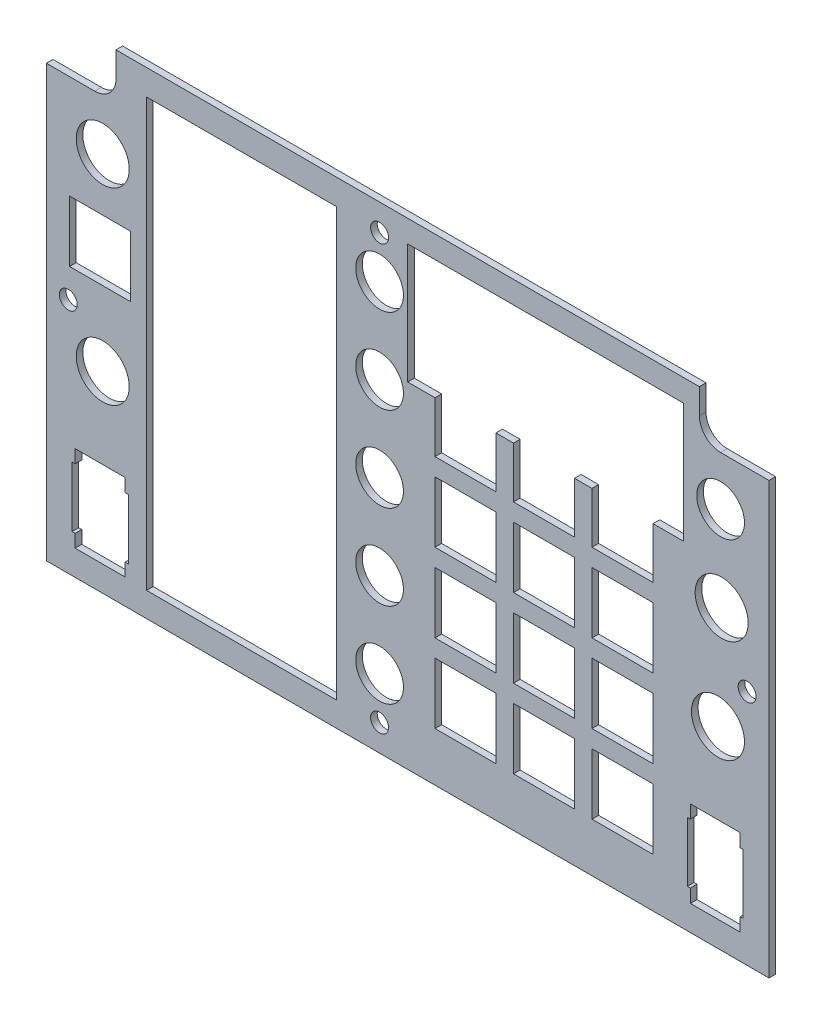
SolidWorks part; units mm, degrees
material "ABS PC"
ref_plane "Front Plane" through (0, 0, 0) normal (0, 0, 1) x (1, 0, 0)
ref_plane "Top Plane" through (0, 0, 0) normal (0, 1, 0) x (1, 0, 0)
ref_plane "Right Plane" through (0, 0, 0) normal (1, 0, 0) x (0, 0, -1)
sketch "Sketch1" plane through (0, 0, 0) normal (0, 0, 1) x (1, 0, 0)
  line L8 (58.2068, 169.534) -> (58.2068, 175.5665)
  line L9 (58.2068, 175.5665) -> (-81.4932, 175.5665)
  line L10 (-81.4932, 175.5665) -> (-81.4932, 169.534)
  line L11 (-86.5732, 164.454) -> (-98.162, 164.454)
  line L12 (-98.162, 164.454) -> (-98.162, 61.2665)
  line L13 (-98.162, 61.2665) -> (74.8755, 61.2665)
  line L14 (74.8755, 61.2665) -> (74.8755, 164.454)
  line L15 (74.8755, 164.454) -> (63.2868, 164.454)
  line L16 (58.2068, 169.534) -> (58.2068, 175.5665)
  line L17 (58.2068, 175.5665) -> (-81.4932, 175.5665)
  line L18 (-81.4932, 175.5665) -> (-81.4932, 169.534)
  line L19 (-86.5732, 164.454) -> (-98.162, 164.454)
  line L20 (-98.162, 164.454) -> (-98.162, 61.2665)
  line L21 (-98.162, 61.2665) -> (74.8755, 61.2665)
  line L22 (74.8755, 61.2665) -> (74.8755, 164.454)
  line L23 (74.8755, 164.454) -> (63.2868, 164.454)
  arc A2 (58.2068, 169.534) -> (63.2868, 164.454) centre (63.2868, 169.534) ccw
  arc A3 (-86.5732, 164.454) -> (-81.4932, 169.534) centre (-86.5732, 169.534) ccw
  arc A4 (58.2068, 169.534) -> (63.2868, 164.454) centre (63.2868, 169.534) ccw
  arc A5 (-86.5732, 164.454) -> (-81.4932, 169.534) centre (-86.5732, 169.534) ccw
  dimension "D1" = 0
extrude "Boss-Extrude1" add sketch "Sketch1" along normal blind 1.5875
sketch "Sketch2" plane through (0, 0, 1.5875) normal (0, 0, 1) x (1, 0, 0)
  line L4 (67.9868, 67.3295) -> (67.9868, 87.9695)
  line L5 (56.0468, 67.3295) -> (67.9868, 67.3295)
  line L6 (56.0468, 87.9695) -> (56.0468, 67.3295)
  line L7 (67.9868, 87.9695) -> (56.0468, 87.9695)
  line L8 (67.9868, 67.3295) -> (67.9868, 87.9695)
  line L9 (56.0468, 67.3295) -> (67.9868, 67.3295)
  line L10 (56.0468, 87.9695) -> (56.0468, 67.3295)
  line L11 (67.9868, 87.9695) -> (56.0468, 87.9695)
  line L26 (32.4893, 73.014) -> (47.0943, 73.014)
  line L27 (32.4893, 87.619) -> (32.4893, 73.014)
  line L28 (47.0943, 87.619) -> (32.4893, 87.619)
  line L29 (47.0943, 73.014) -> (47.0943, 87.619)
  line L30 (32.4893, 73.014) -> (47.0943, 73.014)
  line L31 (32.4893, 87.619) -> (32.4893, 73.014)
  line L32 (47.0943, 87.619) -> (32.4893, 87.619)
  line L33 (47.0943, 73.014) -> (47.0943, 87.619)
  line L34 (32.4893, 91.81) -> (47.0943, 91.81)
  line L35 (32.4893, 106.415) -> (32.4893, 91.81)
  line L36 (47.0943, 106.415) -> (32.4893, 106.415)
  line L37 (47.0943, 91.81) -> (47.0943, 106.415)
  line L38 (32.4893, 91.81) -> (47.0943, 91.81)
  line L39 (32.4893, 106.415) -> (32.4893, 91.81)
  line L40 (47.0943, 106.415) -> (32.4893, 106.415)
  line L41 (47.0943, 91.81) -> (47.0943, 106.415)
  line L42 (32.4893, 110.606) -> (47.0943, 110.606)
  line L43 (32.4893, 125.211) -> (32.4893, 110.606)
  line L44 (47.0943, 125.211) -> (32.4893, 125.211)
  line L45 (47.0943, 110.606) -> (47.0943, 125.211)
  line L46 (32.4893, 110.606) -> (47.0943, 110.606)
  line L47 (32.4893, 125.211) -> (32.4893, 110.606)
  line L48 (47.0943, 125.211) -> (32.4893, 125.211)
  line L49 (47.0943, 110.606) -> (47.0943, 125.211)
  line L51 (13.6933, 73.014) -> (28.2983, 73.014)
  line L52 (13.6933, 87.619) -> (13.6933, 73.014)
  line L53 (28.2983, 87.619) -> (13.6933, 87.619)
  line L54 (28.2983, 73.014) -> (28.2983, 87.619)
  line L55 (13.6933, 73.014) -> (28.2983, 73.014)
  line L56 (13.6933, 87.619) -> (13.6933, 73.014)
  line L57 (28.2983, 87.619) -> (13.6933, 87.619)
  line L58 (28.2983, 73.014) -> (28.2983, 87.619)
  line L59 (13.6933, 91.81) -> (28.2983, 91.81)
  line L60 (13.6933, 106.415) -> (13.6933, 91.81)
  line L61 (28.2983, 106.415) -> (13.6933, 106.415)
  line L62 (32.4893, 141.6095) -> (32.4893, 129.402)
  line L63 (28.2983, 141.6095) -> (32.4893, 141.6095)
  line L64 (28.2983, 129.402) -> (28.2983, 141.6095)
  line L65 (13.6933, 129.402) -> (28.2983, 129.402)
  line L66 (13.6933, 141.6095) -> (13.6933, 129.402)
  line L67 (9.5023, 141.6095) -> (13.6933, 141.6095)
  line L68 (9.5023, 129.402) -> (9.5023, 141.6095)
  line L69 (-5.1027, 129.402) -> (9.5023, 129.402)
  line L70 (-5.1027, 141.6095) -> (-5.1027, 129.402)
  line L71 (-11.6432, 141.6095) -> (-5.1027, 141.6095)
  line L72 (-11.6432, 170.2495) -> (-11.6432, 141.6095)
  line L73 (54.3968, 170.2495) -> (-11.6432, 170.2495)
  line L74 (54.3968, 141.6095) -> (54.3968, 170.2495)
  line L75 (47.0943, 141.6095) -> (54.3968, 141.6095)
  line L76 (47.0943, 129.402) -> (47.0943, 141.6095)
  line L77 (32.4893, 129.402) -> (47.0943, 129.402)
  line L78 (32.4893, 141.6095) -> (32.4893, 129.402)
  line L79 (28.2983, 141.6095) -> (32.4893, 141.6095)
  line L80 (28.2983, 129.402) -> (28.2983, 141.6095)
  line L81 (13.6933, 129.402) -> (28.2983, 129.402)
  line L82 (13.6933, 141.6095) -> (13.6933, 129.402)
  line L83 (9.5023, 141.6095) -> (13.6933, 141.6095)
  line L84 (9.5023, 129.402) -> (9.5023, 141.6095)
  line L85 (-5.1027, 129.402) -> (9.5023, 129.402)
  line L86 (-5.1027, 141.6095) -> (-5.1027, 129.402)
  line L87 (-11.6432, 141.6095) -> (-5.1027, 141.6095)
  line L88 (-11.6432, 170.2495) -> (-11.6432, 141.6095)
  line L89 (54.3968, 170.2495) -> (-11.6432, 170.2495)
  line L90 (54.3968, 141.6095) -> (54.3968, 170.2495)
  line L91 (47.0943, 141.6095) -> (54.3968, 141.6095)
  line L92 (47.0943, 129.402) -> (47.0943, 141.6095)
  line L93 (32.4893, 129.402) -> (47.0943, 129.402)
  line L94 (28.2983, 91.81) -> (28.2983, 106.415)
  line L95 (13.6933, 91.81) -> (28.2983, 91.81)
  line L96 (13.6933, 106.415) -> (13.6933, 91.81)
  line L97 (28.2983, 106.415) -> (13.6933, 106.415)
  line L98 (28.2983, 91.81) -> (28.2983, 106.415)
  line L99 (13.6933, 110.606) -> (28.2983, 110.606)
  line L100 (13.6933, 125.211) -> (13.6933, 110.606)
  line L101 (28.2983, 125.211) -> (13.6933, 125.211)
  line L102 (28.2983, 110.606) -> (28.2983, 125.211)
  line L103 (13.6933, 110.606) -> (28.2983, 110.606)
  line L104 (13.6933, 125.211) -> (13.6933, 110.606)
  line L105 (28.2983, 125.211) -> (13.6933, 125.211)
  line L106 (28.2983, 110.606) -> (28.2983, 125.211)
  line L107 (9.5023, 125.211) -> (-5.1027, 125.211)
  line L108 (9.5023, 110.606) -> (9.5023, 125.211)
  line L109 (-5.1027, 110.606) -> (9.5023, 110.606)
  line L110 (-5.1027, 125.211) -> (-5.1027, 110.606)
  line L111 (9.5023, 125.211) -> (-5.1027, 125.211)
  line L112 (9.5023, 110.606) -> (9.5023, 125.211)
  line L113 (-5.1027, 110.606) -> (9.5023, 110.606)
  line L114 (-5.1027, 125.211) -> (-5.1027, 110.606)
  line L115 (-5.1027, 91.81) -> (9.5023, 91.81)
  line L116 (-5.1027, 106.415) -> (-5.1027, 91.81)
  line L117 (9.5023, 106.415) -> (-5.1027, 106.415)
  line L118 (9.5023, 91.81) -> (9.5023, 106.415)
  line L119 (-5.1027, 91.81) -> (9.5023, 91.81)
  line L120 (-5.1027, 106.415) -> (-5.1027, 91.81)
  line L121 (9.5023, 106.415) -> (-5.1027, 106.415)
  line L122 (9.5023, 91.81) -> (9.5023, 106.415)
  line L123 (-5.1027, 73.014) -> (9.5023, 73.014)
  line L124 (-5.1027, 87.619) -> (-5.1027, 73.014)
  line L125 (9.5023, 87.619) -> (-5.1027, 87.619)
  line L126 (9.5023, 73.014) -> (9.5023, 87.619)
  line L127 (-5.1027, 73.014) -> (9.5023, 73.014)
  line L128 (-5.1027, 87.619) -> (-5.1027, 73.014)
  line L129 (9.5023, 87.619) -> (-5.1027, 87.619)
  line L130 (9.5023, 73.014) -> (9.5023, 87.619)
  line L131 (-78.0007, 139.689) -> (-92.6057, 139.689)
  line L132 (-78.0007, 125.084) -> (-78.0007, 139.689)
  line L133 (-92.6057, 125.084) -> (-78.0007, 125.084)
  line L134 (-92.6057, 139.689) -> (-92.6057, 125.084)
  line L135 (-78.0007, 139.689) -> (-92.6057, 139.689)
  line L136 (-78.0007, 125.084) -> (-78.0007, 139.689)
  line L137 (-92.6057, 125.084) -> (-78.0007, 125.084)
  line L138 (-92.6057, 139.689) -> (-92.6057, 125.084)
  line L139 (-74.1732, 67.1295) -> (-28.7112, 67.1295)
  line L140 (-74.1732, 169.4495) -> (-74.1732, 67.1295)
  line L141 (-28.7112, 169.4495) -> (-74.1732, 169.4495)
  line L142 (-28.7112, 67.1295) -> (-28.7112, 169.4495)
  line L143 (-74.1732, 67.1295) -> (-28.7112, 67.1295)
  line L144 (-74.1732, 169.4495) -> (-74.1732, 67.1295)
  line L145 (-28.7112, 169.4495) -> (-74.1732, 169.4495)
  line L146 (-28.7112, 67.1295) -> (-28.7112, 169.4495)
  line L147 (-79.3332, 67.3295) -> (-79.3332, 87.9695)
  line L148 (-91.2732, 67.3295) -> (-79.3332, 67.3295)
  line L149 (-91.2732, 87.9695) -> (-91.2732, 67.3295)
  line L150 (-79.3332, 87.9695) -> (-91.2732, 87.9695)
  line L151 (-79.3332, 67.3295) -> (-79.3332, 87.9695)
  line L152 (-91.2732, 67.3295) -> (-79.3332, 67.3295)
  line L153 (-91.2732, 87.9695) -> (-91.2732, 67.3295)
  line L154 (-79.3332, 87.9695) -> (-91.2732, 87.9695)
  circle A0 centre (-84.6682, 152.389) radius 6.35
  circle A1 centre (-84.6682, 107.304) radius 6.35
  circle A2 centre (63.5408, 132.3865) radius 6.35
  circle A3 centre (62.6518, 107.304) radius 6.35
  circle A10 centre (-18.3742, 77.7765) radius 5.715 construction
  circle A11 centre (-18.3742, 98.0965) radius 5.715 construction
  circle A12 centre (-18.3742, 118.4165) radius 5.715 construction
  circle A13 centre (-18.3742, 138.7365) radius 5.715 construction
  circle A14 centre (-18.3742, 159.0565) radius 5.715 construction
  circle A15 centre (-18.3742, 77.7765) radius 5.715
  circle A16 centre (-18.3742, 98.0965) radius 5.715
  circle A17 centre (-18.3742, 118.4165) radius 5.715
  circle A18 centre (-18.3742, 138.7365) radius 5.715
  circle A19 centre (-18.3742, 159.0565) radius 5.715
  circle A20 centre (63.2868, 152.7065) radius 5.715 construction
  circle A21 centre (63.2868, 152.7065) radius 5.715
  dimension "D1" = 12.7
  dimension "D2" = 0
  dimension "D3" = 0
  dimension "D4" = 0
  dimension "D5" = 0
  dimension "D6" = 0
  dimension "D7" = 0
  dimension "D8" = 0
  dimension "D9" = 0
  dimension "D10" = 0
  dimension "D11" = 0
  dimension "D12" = 0
  dimension "D13" = 0
  dimension "D14" = 0
  dimension "D15" = 0
extrude "Cut-Extrude1" cut sketch "Sketch2" against normal through all
hole_wizard "#6 Clearance Hole2" positions "Sketch5" profile "Sketch6" hole size "#6" standard "ANSI Inch" end condition through all
sketch "Sketch5" plane through (-11.6432, -6.6627, -3.175) normal (0, 0, -1) x (-1, 0, 0)
  point P0 (-81.28, 124.6982)
  point P3 (6.731, 175.8792)
  point P6 (81.28, 124.6982)
  point P9 (6.731, 74.2792)
sketch "Sketch6" plane through (69.6368, 118.0355, -3.175) normal (1, 0, 0) x (0, 1, 0)
  line L0 (0, 0) -> (0, 4.7625)
  line L1 (0, 4.7625) -> (2.1526, 4.7625)
  line L2 (2.1526, 4.7625) -> (2.1526, 0)
  line L3 (2.1526, 0) -> (0, 0)
  line L4 (0, -6.35) -> (0, 107.95) construction
  dimension "Thru Hole Dia." = 4.3053
  dimension "Thru Hole Depth" = 4.7625
sketch "Sketch7" plane through (0, 0, 1.5875) normal (0, 0, 1) x (1, 0, 0)
  line L1 (55.3386, 84.8302) -> (68.6714, 84.8302)
  line L2 (55.3386, 84.8302) -> (55.3386, 70.5174)
  line L3 (55.3386, 70.5174) -> (68.6714, 70.5174)
  line L4 (68.6714, 84.8302) -> (68.6714, 70.5174)
  line L5 (-78.4913, 70.4042) -> (-92.0203, 70.4042)
  line L6 (-78.4913, 70.4042) -> (-78.4913, 84.8288)
  line L7 (-78.4913, 84.8288) -> (-92.0203, 84.8288)
  line L8 (-92.0203, 70.4042) -> (-92.0203, 84.8288)
extrude "Cut-Extrude2" cut sketch "Sketch7" against normal up to next
